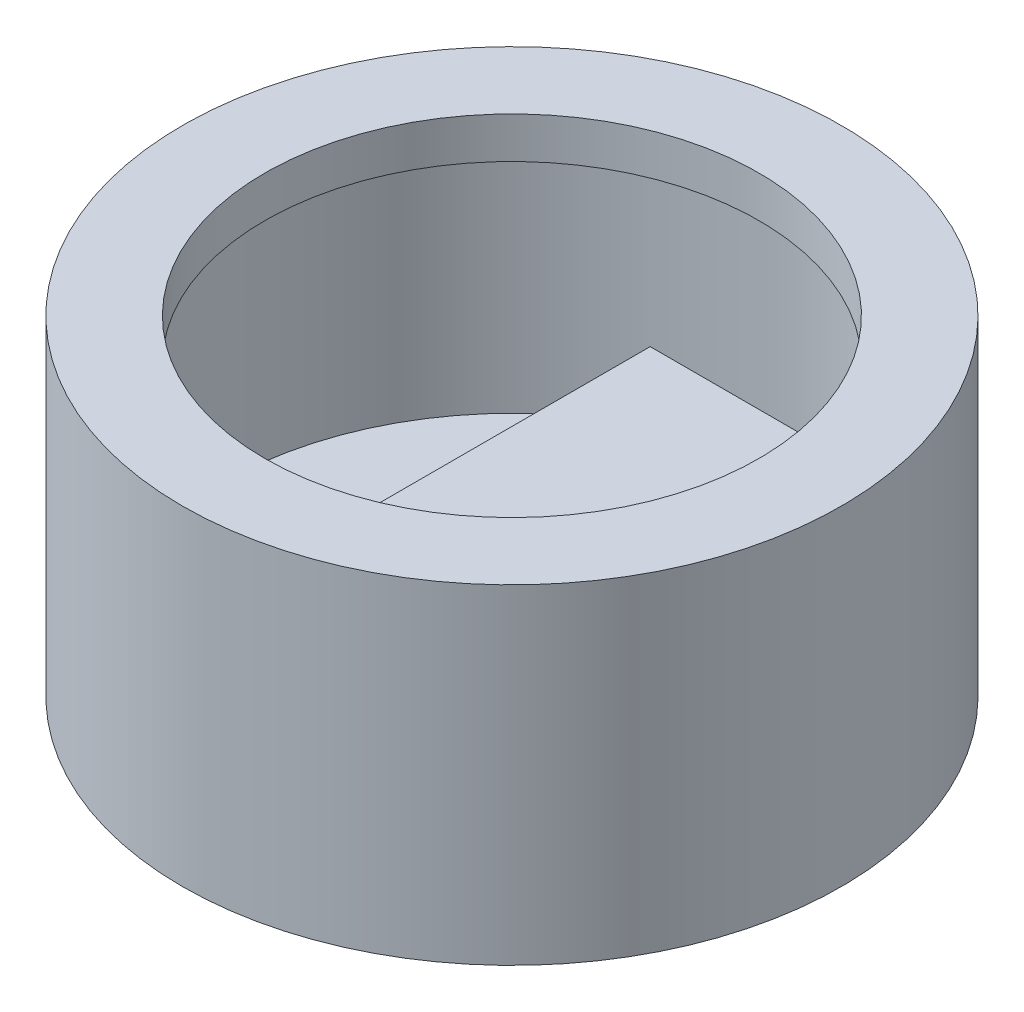
SolidWorks part; units mm, degrees
ref_plane "Front Plane" through (0, 0, 0) normal (0, 0, 1) x (1, 0, 0)
ref_plane "Top Plane" through (0, 0, 0) normal (0, 1, 0) x (1, 0, 0)
ref_plane "Right Plane" through (0, 0, 0) normal (1, 0, 0) x (0, 0, -1)
sketch "Sketch2" plane through (0, 0, 0) normal (0, 1, 0) x (1, 0, 0)
  circle A0 centre (0, 0) radius 40
  dimension "D1" = 80
extrude "Housing" add sketch "Sketch2" along normal blind 40
sketch "Sketch11" plane through (0, 40, 0) normal (0, 1, 0) x (1, 0, 0)
  circle A0 centre (0, 0) radius 30
  dimension "D1" = 60
sketch "Sketch12" plane through (0, 0, 0) normal (0, -1, 0) x (1, 0, 0)
  circle A0 centre (0, 0) radius 35
  dimension "D1" = 70
extrude "ExternalCUt" cut sketch "Sketch11" against normal blind 35
extrude "InternalCut" cut sketch "Sketch12" against normal blind 30 from surface at -5 starting at face at (0, 5, 30)
sketch "Sketch18" plane through (0, 5, 0) normal (0, 1, 0) x (1, 0, 0)
  line L1 (-13.6262, 30.4045) -> (14.3138, 30.4045)
  line L2 (-13.6262, 30.4045) -> (-13.6262, -22.5725)
  line L3 (-13.6262, -22.5725) -> (14.3138, -22.5725)
  line L4 (14.3138, 30.4045) -> (14.3138, -22.5725)
  dimension "D2" = 27.94
extrude "ESP32" add sketch "Sketch18" along normal blind 9.74
sketch "Sketch19" plane through (0, 5, 0) normal (0, 1, 0) x (1, 0, 0)
  circle A0 centre (-25.0066, 0) radius 6
  dimension "D1" = 12
extrude "BuzzerInternalCut" cut sketch "Sketch19" against normal blind 2
sketch "Sketch20" plane through (0, 3, 0) normal (0, 1, 0) x (1, 0, 0)
  circle A0 centre (-26.0423, 4.5223) radius 0.35
  circle A1 centre (-26.0423, 3.0204) radius 0.35
  circle A2 centre (-26.0423, 1.5185) radius 0.35
  circle A3 centre (-26.0423, 0.0167) radius 0.35
  circle A4 centre (-26.0423, -1.4852) radius 0.35
  circle A5 centre (-26.0423, -2.9871) radius 0.35
  circle A6 centre (-26.0423, -4.489) radius 0.35
  circle A7 centre (-24.0423, 4.5223) radius 0.35
  circle A8 centre (-24.0423, 3.0204) radius 0.35
  circle A9 centre (-22.0423, 3.0204) radius 0.35
  circle A10 centre (-28.0423, 3.0204) radius 0.35
  circle A11 centre (-24.0423, 1.5185) radius 0.35
  circle A12 centre (-22.0423, 1.5185) radius 0.35
  circle A13 centre (-20.0423, 1.5185) radius 0.35
  circle A14 centre (-28.0423, 1.5185) radius 0.35
  circle A15 centre (-30.0423, 1.5185) radius 0.35
  circle A16 centre (-24.0423, 0.0167) radius 0.35
  circle A17 centre (-22.0423, 0.0167) radius 0.35
  circle A18 centre (-20.0423, 0.0167) radius 0.35
  circle A19 centre (-24.0423, -1.4852) radius 0.35
  circle A20 centre (-22.0423, -1.4852) radius 0.35
  circle A21 centre (-20.0423, -1.4852) radius 0.35
  circle A22 centre (-24.0423, -2.9871) radius 0.35
  circle A23 centre (-22.0423, -2.9871) radius 0.35
  circle A24 centre (-24.0423, -4.489) radius 0.35
  circle A25 centre (-28.0423, -2.9871) radius 0.35
  circle A26 centre (-28.0423, -1.4852) radius 0.35
  circle A27 centre (-30.0423, -1.4852) radius 0.35
  circle A28 centre (-28.0423, 0.0167) radius 0.35
  circle A29 centre (-30.0423, 0.0167) radius 0.35
  dimension "D1" = 0.7
  dimension "D2" = 7
  dimension "D3" = 2
  dimension "D4" = 3
  dimension "D5" = 2
  dimension "D6" = 4
  dimension "D7" = 3
  dimension "D8" = 4
  dimension "D9" = 4
  dimension "D10" = 3
  dimension "D11" = 2
  dimension "D12" = 2
  dimension "D13" = 3
  dimension "D14" = 3
extrude "BuzzerExtrenalCut" cut sketch "Sketch20" against normal through all contours A7 | A1 | A10 | A15 | A29 | A27 | A28 | A14 | A26 | A25 | A3 | A2 | A4 | A5 | A6 | A24 | A22 | A19 | A16 | A11 | A8 | A9 | A12 | A17 | A20 | A23 | A21 | A18 | A13 | A0
sketch "Sketch22" plane through (0, 5, 0) normal (0, 1, 0) x (1, 0, 0)
  line L1 (20.9886, -8.8883) -> (25.5886, -8.8883)
  line L2 (20.9886, -8.8883) -> (20.9886, -14.9883)
  line L3 (20.9886, -14.9883) -> (25.5886, -14.9883)
  line L4 (25.5886, -8.8883) -> (25.5886, -14.9883)
  dimension "D1" = 6.1
  dimension "D2" = 4.6
extrude "BtnIternalCut" cut sketch "Sketch22" against normal blind 2
sketch "Sketch25" plane through (0, 3, 0) normal (0, 1, 0) x (1, 0, 0)
  circle A0 centre (23.2886, -11.9383) radius 1.5
  dimension "D1" = 3
  dimension "D2" = 2.3
  dimension "D3" = 3.05
extrude "BtnExtrernalCut" cut sketch "Sketch25" against normal through all
sketch "Sketch26" plane through (0, 5, 0) normal (0, 1, 0) x (1, 0, 0)
  line L1 (21.559, 17.8491) -> (25.259, 17.8491)
  line L2 (21.559, 17.8491) -> (21.559, 9.3491)
  line L3 (21.559, 9.3491) -> (25.259, 9.3491)
  line L4 (25.259, 17.8491) -> (25.259, 9.3491)
  dimension "D1" = 3.7
  dimension "D2" = 8.5
extrude "Cut-Extrude6" cut sketch "Sketch26" against normal blind 2
sketch "Sketch28" plane through (0, 3, 0) normal (0, 1, 0) x (1, 0, 0)
  line L0 (21.559, 9.3491) -> (25.259, 9.3491) construction
  line L1 (22.559, 15.3991) -> (24.259, 15.3991)
  line L2 (22.559, 15.3991) -> (22.559, 11.7991)
  line L3 (22.559, 11.7991) -> (24.259, 11.7991)
  line L4 (24.259, 15.3991) -> (24.259, 11.7991)
  line L5 (25.259, 17.8491) -> (21.559, 17.8491) construction
  line L7 (21.559, 17.8491) -> (21.559, 9.3491) construction
  dimension "D1" = 1.7
  dimension "D2" = 3.6
  dimension "D3" = 2.45
  dimension "D4" = 2.45
  dimension "D5" = 1
extrude "Cut-Extrude7" cut sketch "Sketch28" against normal through all
sketch "Sketch29" [suppressed] plane through (0, 14.74, 0) normal (0, 1, 0) x (1, 0, 0)
  line L1 (17.4128, -24.1245) -> (-17.0872, -24.1245)
  line L2 (17.4128, -24.1245) -> (17.4128, 26.8755)
  line L3 (17.4128, 26.8755) -> (-17.0872, 26.8755)
  line L4 (-17.0872, -24.1245) -> (-17.0872, 26.8755)
  dimension "D1" = 34.5
  dimension "D2" = 51
extrude "Boss-Extrude1" [suppressed] add sketch "Sketch29" along normal blind 6.3
